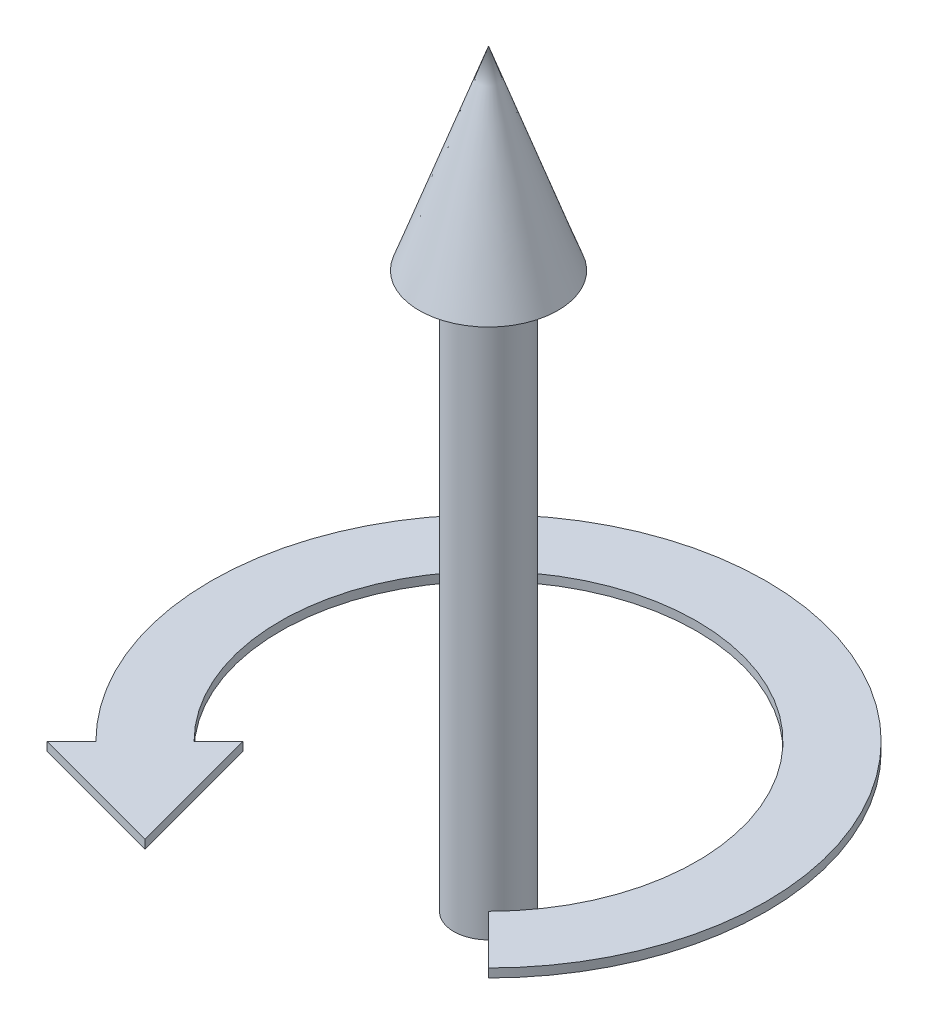
SolidWorks part; units mm, degrees
ref_plane "Front Plane" through (0, 0, 0) normal (0, 0, 1) x (1, 0, 0)
ref_plane "Top Plane" through (0, 0, 0) normal (0, 1, 0) x (1, 0, 0)
ref_plane "Right Plane" through (0, 0, 0) normal (1, 0, 0) x (0, 0, -1)
sketch "Sketch1" plane through (0, 0, 0) normal (0, 1, 0) x (1, 0, 0)
  circle A0 centre (0, 0) radius 1.5875
  dimension "D1" = 3.175
extrude "Boss-Extrude1" add sketch "Sketch1" along normal blind 25.4
sketch "Sketch3" plane through (0, 0, 0) normal (0, 0, 1) x (1, 0, 0)
  line L0 (1.5875, 25.4) -> (-1.5875, 25.4) construction
  line L1 (1.5875, 25.4) -> (-1.5875, 25.4) construction
  line L2 (0, 25.4) -> (0, 34.29)
  line L3 (0, 34.29) -> (3.175, 25.4)
  line L4 (3.175, 25.4) -> (1.5875, 25.4)
  line L5 (0, 25.4) -> (1.5875, 25.4)
  dimension "D1" = 8.89
  dimension "D2" = 3.175
revolve "Revolve1" add sketch "Sketch3" angle 360 about L2
sketch "Sketch4" plane through (0, 0, 0) normal (0, -1, 0) x (1, 0, 0)
  line L0 (0, -12.7) -> (0, 0) construction
  line L1 (-8.9803, 8.9803) -> (0, 0) construction
  line L2 (0, 0) -> (8.9803, 8.9803) construction
  line L3 (-6.7352, 6.7352) -> (-5.6127, 5.6127)
  line L4 (-5.6127, 5.6127) -> (-3.9692, 11.7463)
  line L5 (-3.9692, 11.7463) -> (-10.1028, 10.1028)
  line L6 (-10.1028, 10.1028) -> (-8.9803, 8.9803)
  line L7 (6.7352, 6.7352) -> (8.9803, 8.9803)
  arc A0 (-8.9803, 8.9803) -> (8.9803, 8.9803) centre (0, 0) ccw
  arc A1 (-6.7352, 6.7352) -> (6.7352, 6.7352) centre (0, 0) ccw
  dimension "D1" = 3.175
  dimension "D2" = 19.05
  dimension "D3" = 45
  dimension "D4" = 45
  dimension "D5" = 60
  dimension "D6" = 1.5875
extrude "Boss-Extrude2" add sketch "Sketch4" against normal blind 0.3969 from offset 6.35 separate body
